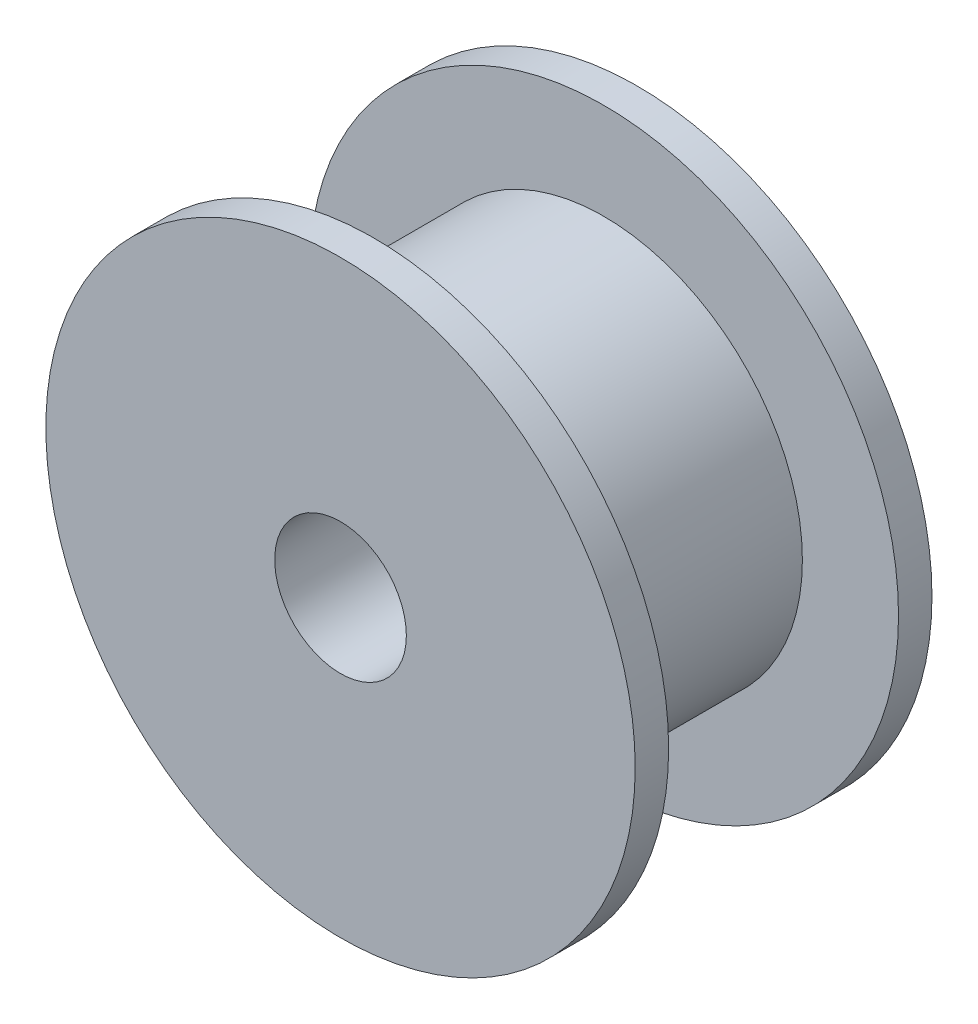
SolidWorks part; units mm, degrees
ref_plane "Front Plane" through (0, 0, 0) normal (0, 0, 1) x (1, 0, 0)
ref_plane "Top Plane" through (0, 0, 0) normal (0, 1, 0) x (1, 0, 0)
ref_plane "Right Plane" through (0, 0, 0) normal (1, 0, 0) x (0, 0, -1)
sketch "Sketch1" plane through (0, 0, 0) normal (0, 0, 1) x (1, 0, 0)
  circle A0 centre (0, 0) radius 8.9535
  circle A1 centre (0, 0) radius 2
  dimension "D1" = 17.907
  dimension "D2" = 4
extrude "Boss-Extrude1" add sketch "Sketch1" along normal blind 1.016
sketch "Sketch2" plane through (0, 0, 1.016) normal (0, 0, 1) x (1, 0, 0)
  circle A20 centre (0, 0) radius 2 construction
  circle A22 centre (0, 0) radius 2
  circle A23 centre (0, 0) radius 6.0325
  dimension "D1" = 12.065
extrude "Boss-Extrude2" add sketch "Sketch2" along normal blind 6.985
sketch "Sketch3" plane through (0, 0, 8.001) normal (0, 0, 1) x (1, 0, 0)
  circle A1 centre (0, 0) radius 8.9535
  circle A2 centre (0, 0) radius 8.9535
  circle A6 centre (0, 0) radius 2 construction
  circle A7 centre (0, 0) radius 2
  dimension "D1" = 0
extrude "Boss-Extrude3" add sketch "Sketch3" along normal blind 1.016
